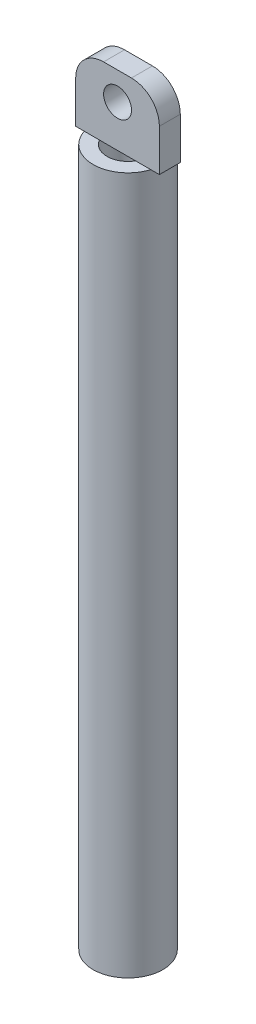
SolidWorks part; units mm, degrees
ref_plane "Front Plane" through (0, 0, 0) normal (0, 0, 1) x (1, 0, 0)
ref_plane "Top Plane" through (0, 0, 0) normal (0, 1, 0) x (1, 0, 0)
ref_plane "Right Plane" through (0, 0, 0) normal (1, 0, 0) x (0, 0, -1)
sketch "Sketch1" plane through (0, 0, 0) normal (0, 1, 0) x (1, 0, 0)
  circle A0 centre (0, 0) radius 1.5
  circle A1 centre (0, 0) radius 2.5
  dimension "D1" = 3
  dimension "D2" = 5
extrude "Boss-Extrude1" add sketch "Sketch1" along normal blind 50
sketch "Sketch2" plane through (0, 50, 0) normal (0, 1, 0) x (1, 0, 0)
  line L1 (-3, 0.75) -> (3, 0.75)
  line L2 (-3, 0.75) -> (-3, -0.75)
  line L3 (-3, -0.75) -> (3, -0.75)
  line L4 (3, 0.75) -> (3, -0.75)
  line L5 (-3, 0.75) -> (3, -0.75) construction
  line L6 (-3, -0.75) -> (3, 0.75) construction
  point P0 (0, 0)
  dimension "D1" = 1.5
  dimension "D2" = 6
extrude "Boss-Extrude2" add sketch "Sketch2" along normal blind 5
sketch "Sketch3" plane through (0, 0, -0.75) normal (0, 0, -1) x (-1, 0, 0)
  line L0 (-3, 55) -> (3, 55) construction
  circle A0 centre (0, 53) radius 1
  dimension "D1" = 2
  dimension "D2" = 2
extrude "Cut-Extrude1" cut sketch "Sketch3" against normal through all
fillet "Fillet1" radius 2 2 edges at (-3, 55, 0) (3, 55, 0)
